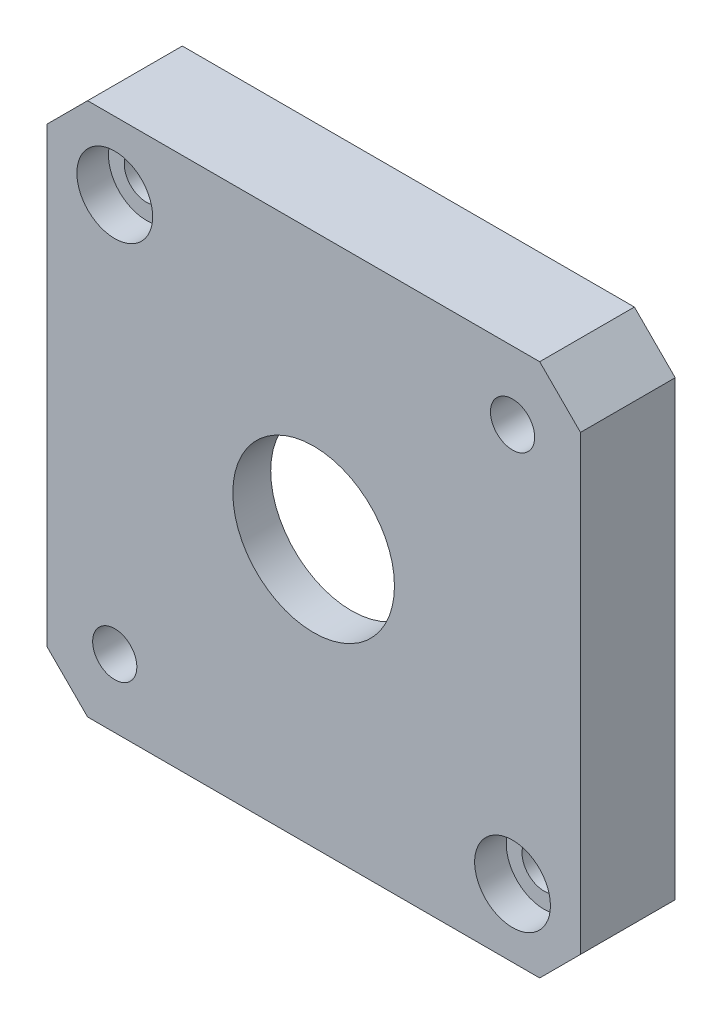
SolidWorks part; units mm, degrees
ref_plane "Front Plane" through (0, 0, 0) normal (0, 0, 1) x (1, 0, 0)
ref_plane "Top Plane" through (0, 0, 0) normal (0, 1, 0) x (1, 0, 0)
ref_plane "Right Plane" through (0, 0, 0) normal (1, 0, 0) x (0, 0, -1)
sketch "Sketch1" plane through (0, 0, 0) normal (0, 0, 1) x (1, 0, 0)
  line L0 (-12.3275, 17.6166) -> (-12.3275, -18.1834)
  line L1 (-12.3275, -18.1834) -> (-9.0952, -21.4157)
  line L2 (-9.0952, -21.4157) -> (26.7048, -21.4157)
  line L3 (26.7048, -21.4157) -> (29.9371, -18.1834)
  line L4 (29.9371, -18.1834) -> (29.9371, 17.6166)
  line L5 (29.9371, 17.6166) -> (26.7048, 20.8489)
  line L6 (26.7048, 20.8489) -> (-9.0952, 20.8489)
  line L7 (-9.0952, 20.8489) -> (-12.3275, 17.6166)
  line L8 (-6.9452, -16.0334) -> (24.5548, 15.4666) construction
  line L9 (24.5548, 15.4666) -> (24.5548, -16.0334) construction
  line L10 (24.5548, -16.0334) -> (-6.9452, -16.0334) construction
  line L11 (-6.9452, -16.0334) -> (-6.9452, 15.4666) construction
  line L12 (-6.9452, 15.4666) -> (24.5548, 15.4666) construction
  line L13 (28.321, 19.2327) -> (24.5548, 15.4666) construction
  line L14 (28.321, -19.7996) -> (24.5548, -16.0334) construction
  line L15 (-10.7113, 19.2327) -> (28.321, -19.7996) construction
  line L16 (-10.7113, -19.7996) -> (28.321, 19.2327) construction
  line L17 (28.321, -19.7996) -> (24.5548, -16.0334) construction
  circle A0 centre (8.8048, -0.2834) radius 18.5
  circle A1 centre (-6.9452, 15.4666) radius 1.75
  circle A2 centre (-6.9452, -16.0334) radius 1.75
  circle A3 centre (24.5548, -16.0334) radius 1.75
  circle A4 centre (24.5548, 15.4666) radius 1.75
  dimension "D1" = 37
  dimension "D2" = 31.5
  dimension "D3" = 31.5
  dimension "D4" = 35.8
  dimension "D5" = 35.8
  dimension "D6" = 35.8
  dimension "D7" = 35.8
  dimension "D8" = 55.2
  dimension "D9" = 55.2
  dimension "D10" = 44.5477
extrude "Boss-Extrude1" add sketch "Sketch1" along normal blind 4.5
sketch "Sketch2" plane through (0, 0, 4.5) normal (0, 0, 1) x (1, 0, 0)
  line L0 (-12.3275, 17.6166) -> (-9.0952, 20.8489)
  line L1 (-9.0952, 20.8489) -> (26.7048, 20.8489)
  line L2 (26.7048, 20.8489) -> (29.9371, 17.6166)
  line L3 (29.9371, 17.6166) -> (29.9371, -18.1834)
  line L4 (29.9371, -18.1834) -> (26.7048, -21.4157)
  line L5 (26.7048, -21.4157) -> (-9.0952, -21.4157)
  line L6 (-9.0952, -21.4157) -> (-12.3275, -18.1834)
  line L7 (-12.3275, -18.1834) -> (-12.3275, 17.6166)
  line L8 (-6.9452, 15.4666) -> (24.5548, -16.0334) construction
  circle A0 centre (8.8048, -0.2834) radius 6.4
  circle A1 centre (-6.9452, 15.4666) radius 1.75
  circle A2 centre (24.5548, 15.4666) radius 1.75
  circle A3 centre (24.5548, -16.0334) radius 1.75
  circle A4 centre (-6.9452, -16.0334) radius 1.75
  dimension "D1" = 12.8
extrude "Boss-Extrude2" add sketch "Sketch2" along normal blind 3
sketch "Sketch3" plane through (0, 0, 7.5) normal (0, 0, 1) x (1, 0, 0)
  circle A0 centre (-6.9452, 15.4666) radius 3
  circle A1 centre (24.5548, -16.0334) radius 3
  dimension "D1" = 6
  dimension "D2" = 6
extrude "Cut-Extrude1" cut sketch "Sketch3" against normal blind 2.5
